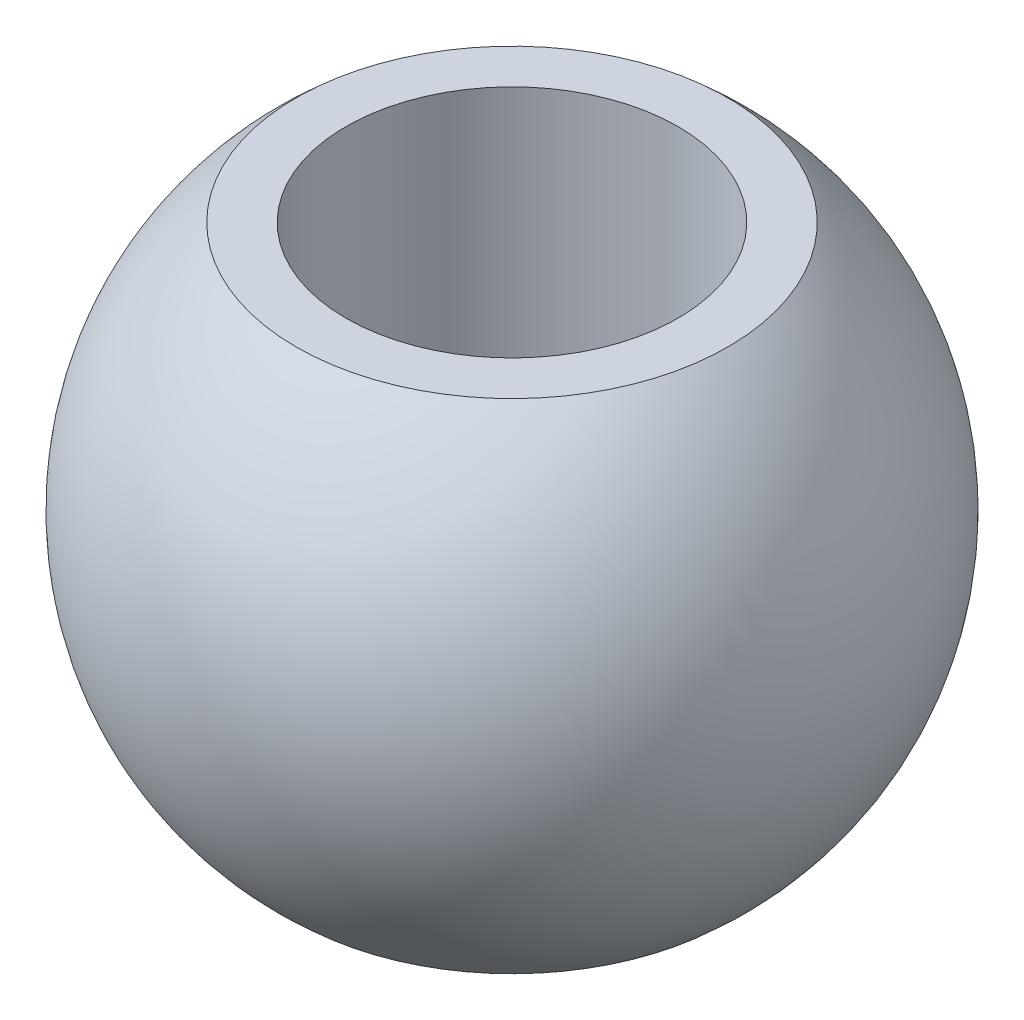
SolidWorks part; units mm, degrees
ref_plane "Front Plane" through (0, 0, 0) normal (0, 0, 1) x (1, 0, 0)
ref_plane "Top Plane" through (0, 0, 0) normal (0, 1, 0) x (1, 0, 0)
ref_plane "Right Plane" through (0, 0, 0) normal (1, 0, 0) x (0, 0, -1)
sketch "Sketch1" plane through (0, 0, 0) normal (0, 0, 1) x (1, 0, 0)
  line L0 (0, 12) -> (0, 0) construction
  line L1 (-5.2, 12) -> (-4, 12)
  line L2 (-4, 12) -> (-4, 0)
  line L3 (-4, 0) -> (-5.2, 0)
  arc A1 (-5.2, 12) -> (-5.2, 0) centre (-0.0035, 6) ccw
  dimension "D1" = 4
  dimension "D3" = 7.9375
  dimension "D2" = 12
  dimension "D4" = 5.2
revolve "Revolve1" add sketch "Sketch1" angle 360 about L0
ref_plane "Plane1" through (0, 6, 0) normal (0, 1, 0) x (1, 0, 0)
sketch "Sketch2" plane through (0, 6, 0) normal (0, 1, 0) x (1, 0, 0)
  point P0 (0, 0)
